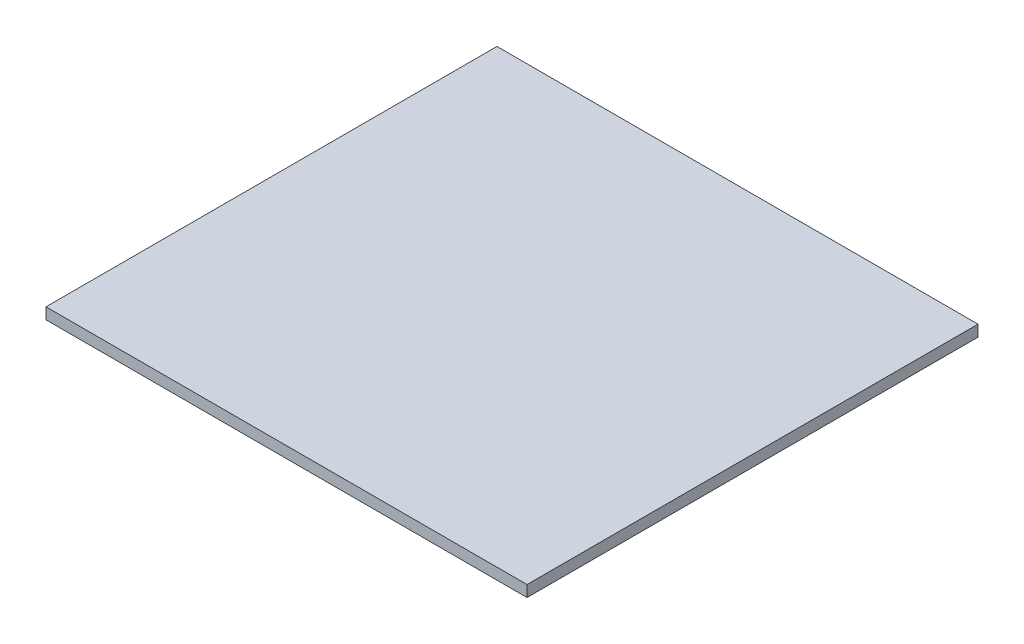
SolidWorks part; units mm, degrees
ref_plane "Front Plane" through (0, 0, 0) normal (0, 0, 1) x (1, 0, 0)
ref_plane "Top Plane" through (0, 0, 0) normal (0, 1, 0) x (1, 0, 0)
ref_plane "Right Plane" through (0, 0, 0) normal (1, 0, 0) x (0, 0, -1)
sketch "Sketch1" plane through (0, 0, 0) normal (0, 1, 0) x (1, 0, 0)
  line L1 (0, 0) -> (203.2, 0)
  line L2 (0, 0) -> (0, -190.5)
  line L3 (0, -190.5) -> (203.2, -190.5)
  line L4 (203.2, 0) -> (203.2, -190.5)
  dimension "D1" = 190.5
  dimension "D2" = 203.2
extrude "Boss-Extrude1" add sketch "Sketch1" along normal blind 4.7625 contours L1 L4 L3 L2
